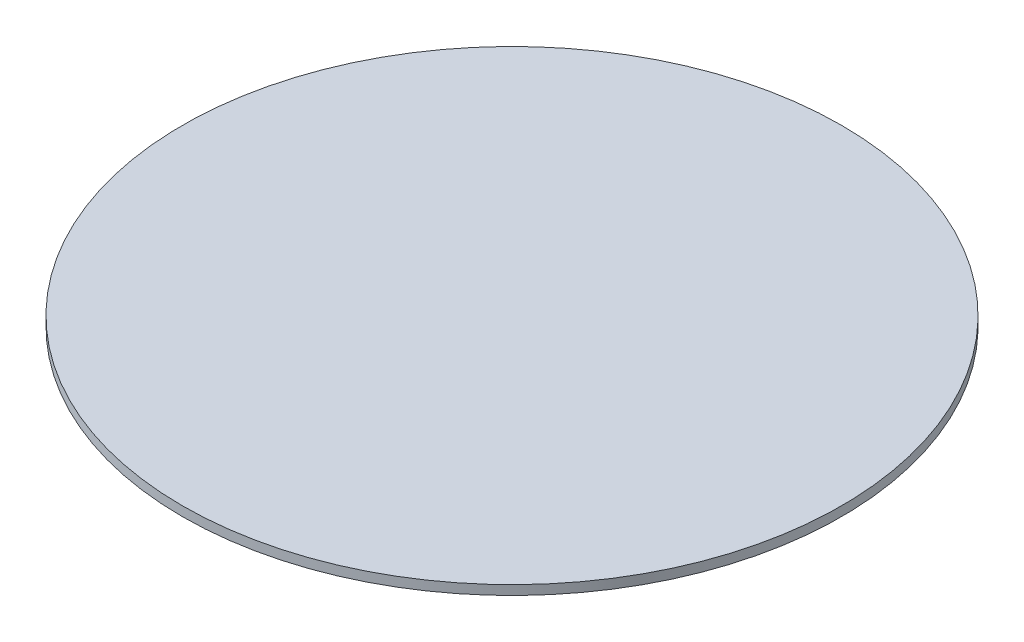
SolidWorks part; units mm, degrees
ref_plane "Piano frontale" through (0, 0, 0) normal (0, 0, 1) x (1, 0, 0)
ref_plane "Piano superiore" through (0, 0, 0) normal (0, 1, 0) x (1, 0, 0)
ref_plane "Piano destro" through (0, 0, 0) normal (1, 0, 0) x (0, 0, -1)
sketch "Schizzo1" plane through (0, 0, 0) normal (0, 1, 0) x (1, 0, 0)
  circle A0 centre (0, 0) radius 10.5
  dimension "D1" = 21
extrude "Estrusione-Estrusione1" add sketch "Schizzo1" along normal blind 0.3
